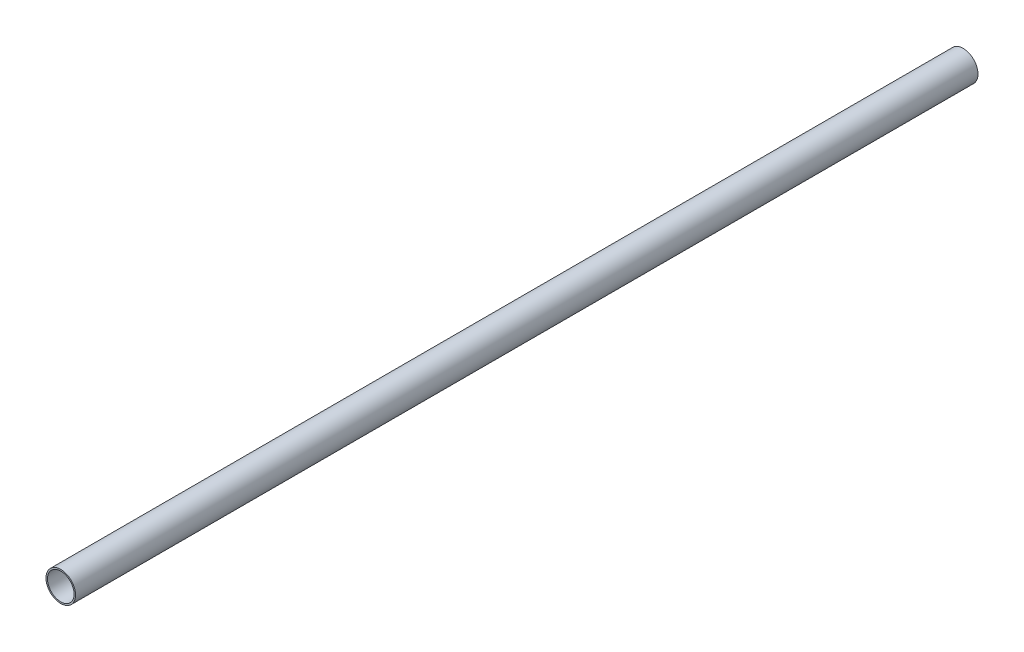
SolidWorks part; units mm, degrees
material "1060 Alloy"
ref_plane "Front Plane" through (0, 0, 0) normal (0, 0, 1) x (1, 0, 0)
ref_plane "Top Plane" through (0, 0, 0) normal (0, 1, 0) x (1, 0, 0)
ref_plane "Right Plane" through (0, 0, 0) normal (1, 0, 0) x (0, 0, -1)
sketch "Sketch1" plane through (0, 0, 0) normal (0, 0, 1) x (1, 0, 0)
  circle A0 centre (0, 0) radius 12.7
  circle A1 centre (0, 0) radius 11.43
  dimension "D1" = 25.4
  dimension "D2" = 1.27
extrude "Boss-Extrude1" add sketch "Sketch1" along normal blind 774.7
